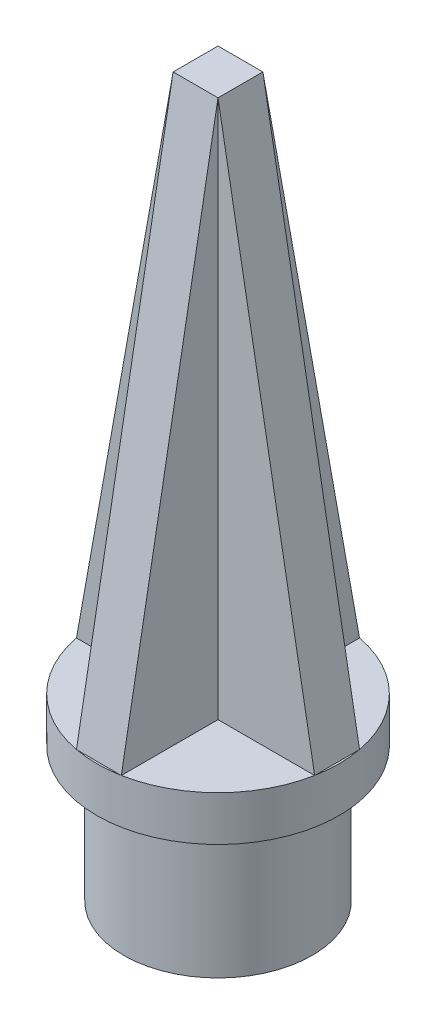
SolidWorks part; units mm, degrees
ref_plane "Front Plane" through (0, 0, 0) normal (0, 0, 1) x (1, 0, 0)
ref_plane "Top Plane" through (0, 0, 0) normal (0, 1, 0) x (1, 0, 0)
ref_plane "Right Plane" through (0, 0, 0) normal (1, 0, 0) x (0, 0, -1)
sketch "Sketch1" plane through (0, 0, 0) normal (0, 1, 0) x (1, 0, 0)
  circle A0 centre (0, 0) radius 10.5
  dimension "D1" = 21
extrude "Boss-Extrude1" add sketch "Sketch1" along normal blind 15
sketch "Sketch5" plane through (0, 0, 0) normal (0, -1, 0) x (1, 0, 0)
  circle A0 centre (0, 0) radius 10.5
  point P3 (0, 0)
sketch "Sketch6" plane through (0, 15, 0) normal (0, 1, 0) x (1, 0, 0)
  circle A0 centre (0, 0) radius 13.5
  dimension "D1" = 27
extrude "Boss-Extrude4" add sketch "Sketch6" along normal blind 5
sketch "Sketch10" plane through (0, 0, 0) normal (0, -1, 0) x (1, 0, 0)
  circle A0 centre (0, 0) radius 7.5
  circle A1 centre (0, 0) radius 10.5 construction
  dimension "D1" = 3
sketch "Sketch12" plane through (0, 20, 0) normal (0, 1, 0) x (1, 0, 0)
  line L0 (2.5, -2.5) -> (13.2665, -2.5)
  line L1 (-2.5, 13.2665) -> (2.5, 13.2665)
  line L2 (-2.5, 13.2665) -> (-2.5, 2.5)
  line L3 (-2.5, -13.2665) -> (2.5, -13.2665)
  line L4 (2.5, 13.2665) -> (2.5, 2.5)
  line L5 (-13.2665, 2.5) -> (-2.5, 2.5)
  line L6 (-13.2665, 2.5) -> (-13.2665, -2.5)
  line L7 (-13.2665, -2.5) -> (-2.5, -2.5)
  line L8 (13.2665, 2.5) -> (13.2665, -2.5)
  line L9 (-2.5, -2.5) -> (-2.5, -13.2665)
  line L10 (2.5, 2.5) -> (13.2665, 2.5)
  line L11 (2.5, -2.5) -> (2.5, -13.2665)
  circle A0 centre (0, 0) radius 13.5 construction
  dimension "D1" = 5
  dimension "D2" = 5
  dimension "D3" = 2.5
  dimension "D4" = 2.5
extrude "Boss-Extrude6" add sketch "Sketch12" along normal blind 60
sketch "Sketch16" plane through (0, 0, 0) normal (0, 0, 1) x (1, 0, 0)
  line L0 (0, 0) -> (0, 93.3241) construction
extrude "Cut-Extrude5" cut sketch "Sketch10" against normal up to surface (15 mm away) up to face at (0, 15, 10.5)
sketch "Sketch17" plane through (-2.5, 0, 0) normal (-1, 0, 0) x (0, 0, 1)
  line L0 (-13.2665, 80) -> (-13.2665, 20)
  line L1 (-13.2665, 20) -> (-2.5, 80)
  line L2 (-2.5, 80) -> (-13.2665, 80)
  line L3 (2.5, 80) -> (13.2665, 20)
  line L6 (2.5, 80) -> (13.2665, 80)
  line L7 (13.2665, 80) -> (13.2665, 20)
extrude "Cut-Extrude6" cut sketch "Sketch17" against normal up to next
sketch "Sketch18" plane through (0, 0, -2.5) normal (0, 0, -1) x (-1, 0, 0)
  line L0 (2.5, 80) -> (13.2665, 20)
  line L3 (-2.5, 80) -> (-13.2665, 20)
  line L4 (-13.2665, 20) -> (-13.2665, 80)
  line L5 (-13.2665, 80) -> (-2.5, 80)
  line L6 (2.5, 80) -> (13.2665, 80)
  line L7 (13.2665, 80) -> (13.2665, 66.4864)
  line L8 (13.2665, 80) -> (13.2665, 20) construction
  line L9 (13.2665, 66.4864) -> (13.2665, 20)
extrude "Cut-Extrude7" cut sketch "Sketch18" against normal up to next
